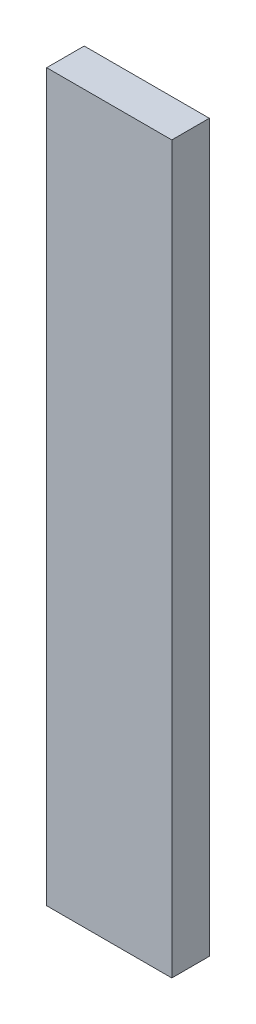
SolidWorks part; units mm, degrees
ref_plane "Plan de face" through (0, 0, 0) normal (0, 0, 1) x (1, 0, 0)
ref_plane "Plan de dessus" through (0, 0, 0) normal (0, 1, 0) x (1, 0, 0)
ref_plane "Plan de droite" through (0, 0, 0) normal (1, 0, 0) x (0, 0, -1)
sketch "Esquisse1" plane through (0, 0, 0) normal (0, 0, 1) x (1, 0, 0)
  line L1 (-10, 78) -> (10, 78)
  line L2 (-10, 78) -> (-10, -38)
  line L3 (-10, -38) -> (10, -38)
  line L4 (10, 78) -> (10, -38)
  dimension "D1" = 116
  dimension "D2" = 20
  dimension "D3" = 10
  dimension "D4" = 38
extrude "Boss.-Extru.1" add sketch "Esquisse1" along normal blind 6
equation "\"D3@Esquisse1\"=\"D2@Esquisse1\"/2"
equation "\"D4@Esquisse1\"=\"D1@Esquisse1\"/2"
